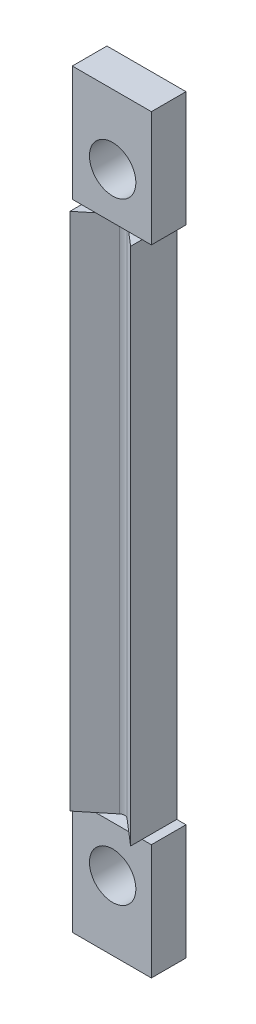
SolidWorks part; units mm, degrees
ref_plane "Front Plane" through (0, 0, 0) normal (0, 0, 1) x (1, 0, 0)
ref_plane "Top Plane" through (0, 0, 0) normal (0, 1, 0) x (1, 0, 0)
ref_plane "Right Plane" through (0, 0, 0) normal (1, 0, 0) x (0, 0, -1)
sketch "Sketch1" plane through (0, 0, 0) normal (0, 1, 0) x (1, 0, 0)
  line L0 (0, 0) -> (-2.6946, -2.2)
  line L1 (0, 0) -> (2.5554, -2.2)
  line L2 (-2.6946, -2.2) -> (-2.6946, 1.8)
  line L3 (-2.6946, 1.8) -> (2.5554, 1.8)
  line L4 (2.5554, 1.8) -> (2.5554, -2.2)
  dimension "D1" = 5.25
  dimension "D2" = 2.2
  dimension "D3" = 4
extrude "Boss-Extrude1" add sketch "Sketch1" along normal mid plane 45
sketch "Sketch2" plane through (0, 22.5, 0) normal (0, 1, 0) x (1, 0, 0)
  line L1 (-3.4946, 1.8) -> (3.3554, 1.8)
  line L2 (-3.4946, 1.8) -> (-3.4946, -1.2)
  line L3 (-3.4946, -1.2) -> (3.3554, -1.2)
  line L4 (3.3554, 1.8) -> (3.3554, -1.2)
  point P6 (0, 0)
  dimension "D1" = 0.8
  dimension "D2" = 0.8
  dimension "D3" = 3
extrude "Boss-Extrude2" add sketch "Sketch2" along normal blind 10
sketch "Sketch3" plane through (0, -22.5, 0) normal (0, -1, 0) x (1, 0, 0)
  line L1 (-3.4946, -1.8) -> (3.3554, -1.8)
  line L2 (-3.4946, -1.8) -> (-3.4946, 1.2)
  line L3 (-3.4946, 1.2) -> (3.3554, 1.2)
  line L4 (3.3554, -1.8) -> (3.3554, 1.2)
extrude "Boss-Extrude3" add sketch "Sketch3" along normal blind 10
fillet "Fillet2" radius 0.5 1 edges at (0, 0, 0)
sketch "Sketch5" plane through (0, 0, -1.8) normal (0, 0, -1) x (-1, 0, 0)
  line L0 (0, 26.5) -> (0, -26.5) construction
  circle A0 centre (0, -26.5) radius 2.01
  circle A1 centre (0, 26.5) radius 2.01
  point P4 (0, 0)
  dimension "D2" = 4.02
  dimension "D3" = 4.02
  dimension "D1" = 53
extrude "Cut-Extrude1" cut sketch "Sketch5" against normal blind 10
cosmetic thread "Cosmetic Thread1" parameters "D2"=5.02
cosmetic thread "Cosmetic Thread2" parameters "D2"=5.02
